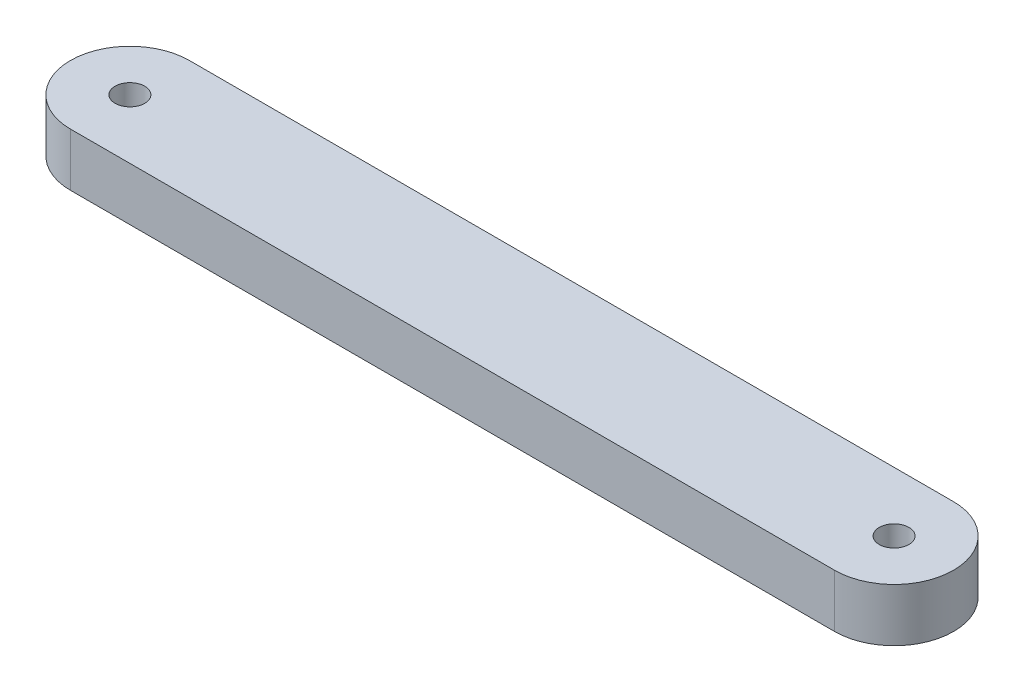
SolidWorks part; units mm, degrees
ref_plane "前视基准面" through (0, 0, 0) normal (0, 0, 1) x (1, 0, 0)
ref_plane "上视基准面" through (0, 0, 0) normal (0, 1, 0) x (1, 0, 0)
ref_plane "右视基准面" through (0, 0, 0) normal (1, 0, 0) x (0, 0, -1)
sketch "草图1" plane through (0, 0, 0) normal (0, 1, 0) x (1, 0, 0)
  line L0 (-259.2308, 0) -> (242.3077, 0) construction
  line L1 (0, 184.2308) -> (0, -188.8462) construction
  line L2 (-180, 28) -> (180, 28)
  line L5 (180, -28) -> (-180, -28)
  circle A0 centre (-180, 0) radius 7
  circle A1 centre (-180, 0) radius 28
  circle A2 centre (180, 0) radius 7
  circle A3 centre (180, 0) radius 28
  dimension "D2" = 14
  dimension "D3" = 56
  dimension "D1" = 180
extrude "凸台-拉伸1" add sketch "草图1" along normal blind 25 contours L5 A3 L2 A1 | A3 A2 | A1 A0
